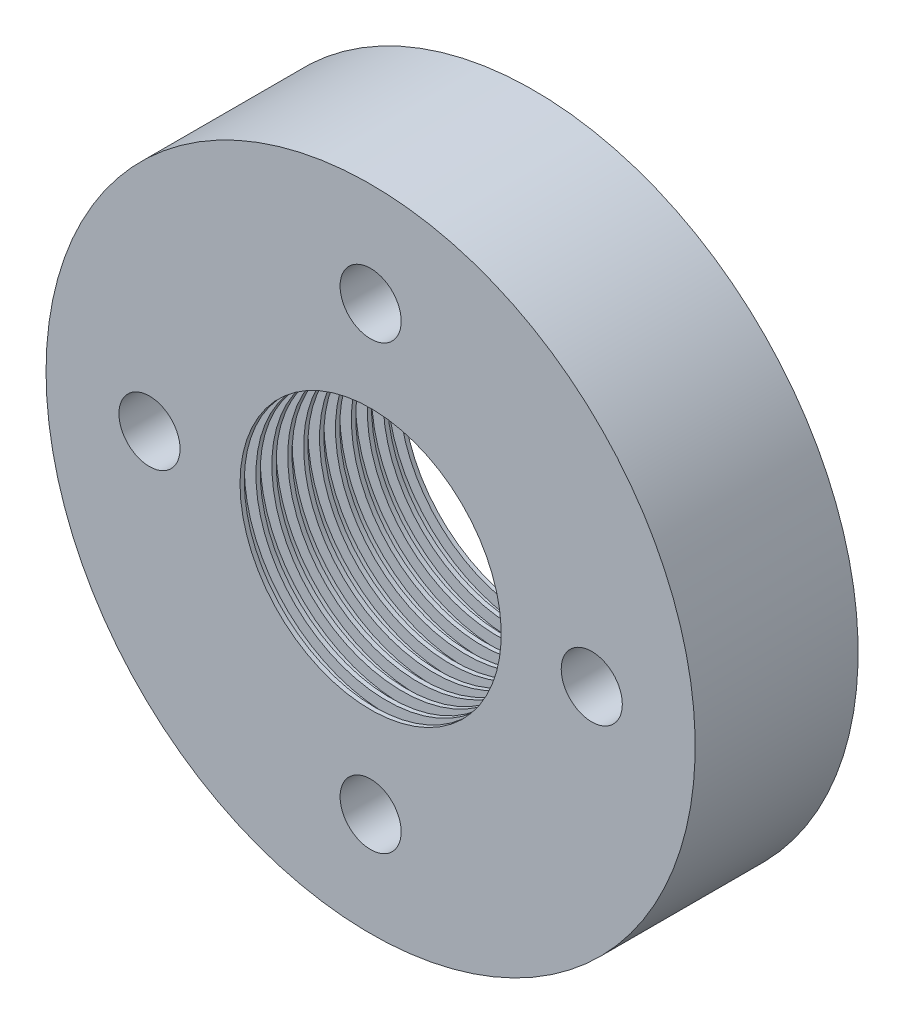
SolidWorks part; units mm, degrees
ref_plane "Front Plane" through (0, 0, 0) normal (0, 0, 1) x (1, 0, 0)
ref_plane "Top Plane" through (0, 0, 0) normal (0, 1, 0) x (1, 0, 0)
ref_plane "Right Plane" through (0, 0, 0) normal (1, 0, 0) x (0, 0, -1)
sketch "Sketch1" plane through (0, 0, 0) normal (1, 0, 0) x (0, 0, -1)
  line L0 (-10.668, 8.5508) -> (-10.668, 21.2508)
  line L1 (-10.668, 21.2508) -> (0, 21.2508)
  line L2 (0, 21.2508) -> (0, 8.5508)
  line L3 (0, 8.5508) -> (-10.668, 8.5508)
  line L4 (0, 0) -> (-6.0752, 0) construction
  line L5 (0, 8.5508) -> (0, 0) construction
  dimension "D1" = 8.5508
  dimension "D2" = 12.7
  dimension "D3" = 10.668
revolve "Revolve1" add sketch "Sketch1" angle 360 about L4
sketch "Sketch2" plane through (0, 0, 0) normal (1, 0, 0) x (0, 0, -1)
  line L0 (0, -8.5508) -> (0, 8.5508) construction
  line L1 (0, -8.5508) -> (0, 8.5508) construction
  line L2 (-0.254, 8.5508) -> (-1.016, 8.5508)
  line L3 (-1.016, 8.5508) -> (-1.016, 9.3128)
  line L4 (-1.016, 9.3128) -> (-0.254, 9.3128)
  line L5 (-0.254, 9.3128) -> (-0.254, 8.5508)
  line L6 (0, 8.5508) -> (-0.254, 8.5508) construction
  dimension "D1" = 0.254
  dimension "D2" = 0.762
  dimension "D3" = 0.762
ref_axis "Axis1" through (0, 0, 10.668) along (0, 0, -1)
revolve "Cut-Revolve1" cut sketch "Sketch2" angle 360 about axis through (0, 0, 10.668) along (0, 0, -1)
pattern_linear "LPattern1" count 10 spacing 1.0414 along (0, 0, 1) of "Cut-Revolve1"
sketch "Sketch3" plane through (0, 0, 0) normal (0, 0, -1) x (-1, 0, 0)
  line L0 (0, 0) -> (0, 14.478) construction
  point P0 (0, 14.478)
  dimension "D1" = 14.478
hole_wizard "M4x0.7 Tapped Hole1" positions "Sketch3" profile "Sketch4" tap size "M4x0.7" standard "ANSI Metric" end condition up to next
sketch "Sketch4" plane through (0, 14.478, 0) normal (1, 0, 0) x (0, 1, 0)
  line L0 (0, 0) -> (0, 10.668)
  line L1 (0, 10.668) -> (2, 10.668)
  line L2 (2, 10.668) -> (2, 0.025)
  line L3 (2, 0.025) -> (2.025, 0)
  line L5 (2.025, 0) -> (0, 0)
  line L6 (-2, 0.025) -> (-2.025, 0) construction
  line L11 (0, -6.35) -> (0, 107.95) construction
  dimension "Thread Major Dia." = 4
  dimension "Thru Tap Drill Depth" = 10.668
  dimension "Near C'Sink Dia." = 4.05
  dimension "Near C'Sink Angle" = 90
pattern_circular "CirPattern1" count 4 every 90 about axis through (0, 0, 0) along (0, 0, 1) of "M4x0.7 Tapped Hole1"
equation "\"seal_length\"= \"teeth\" * ( \"tooth_width\" + \"cavity_width\" ) + \"tooth_width\""
equation "\"D3@Sketch1\"=\"seal_length\""
equation "\"teeth\"= 10"
equation "\"tooth_width\"= .01in"
equation "\"cavity_width\"= .031in"
equation "\"cavity_depth\"= .031in"
equation "\"D1@LPattern1\"=10"
equation "\"D3@LPattern1\"=\"cavity_width\"+\"tooth_width\""
equation "\"hole_radius\"=0.57"
equation "\"D1@Sketch3\"=\"hole_radius\""
